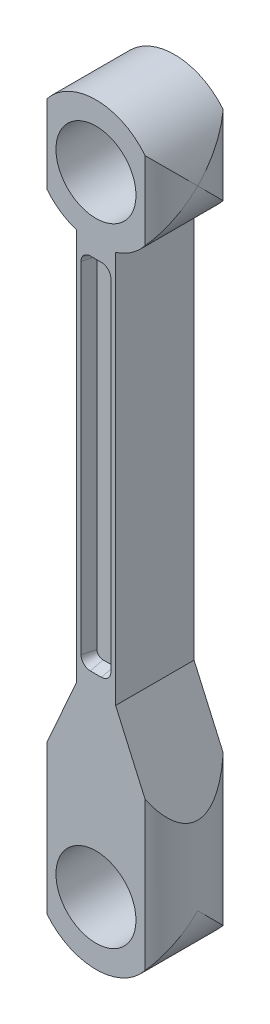
SolidWorks part; units mm, degrees
ref_plane "Front Plane" through (0, 0, 0) normal (0, 0, 1) x (1, 0, 0)
ref_plane "Top Plane" through (0, 0, 0) normal (0, 1, 0) x (1, 0, 0)
ref_plane "Right Plane" through (0, 0, 0) normal (1, 0, 0) x (0, 0, -1)
sketch "Sketch1" plane through (0, 0, 0) normal (0, 0, 1) x (1, 0, 0)
  line L0 (-10.16, 0) -> (-10.16, 12.7)
  line L1 (-10.16, 12.7) -> (-3.1814, 28.448)
  line L2 (-3.1814, 28.448) -> (-3.1814, 91.951)
  line L3 (10.16, 0) -> (10.16, 12.7)
  line L4 (10.16, 12.7) -> (3.1814, 28.448)
  line L5 (3.1814, 28.448) -> (3.1814, 91.951)
  line L6 (10.16, 12.7) -> (10.16, 34.4548) construction
  line L7 (-10.16, 12.7) -> (-10.16, 33.6393) construction
  circle A0 centre (0, 0) radius 6.477
  circle A1 centre (0, 101.6) radius 6.477
  arc A2 (3.1814, 91.951) -> (-3.1814, 91.951) centre (0, 101.6) ccw
  arc A3 (-10.16, 0) -> (10.16, 0) centre (0, 0) ccw
  dimension "D1" = 12.954
  dimension "D2" = 12.954
  dimension "D4" = 20.32
  dimension "D5" = 20.32
  dimension "D3" = 101.6
  dimension "D6" = 23.9
  dimension "D7" = 12.7
  dimension "D8" = 28.448
extrude "Boss-Extrude2" add sketch "Sketch1" along normal blind 12.7
sketch "Sketch3" plane through (0, 0, 12.7) normal (0, 0, 1) x (1, 0, 0)
  line L0 (-3.1814, 91.951) -> (3.1814, 91.951) construction
  line L1 (-3.1814, 28.448) -> (3.1814, 28.448) construction
  line L2 (-3.1814, 91.951) -> (-3.1814, 28.448) construction
  line L3 (-0.8954, 89.408) -> (0.8954, 89.408)
  line L4 (-2.4194, 87.884) -> (-2.4194, 32.766)
  line L5 (-0.8954, 31.242) -> (0.8954, 31.242)
  line L6 (2.4194, 87.884) -> (2.4194, 32.766)
  line L7 (3.1814, 28.448) -> (3.1814, 91.951) construction
  arc A0 (-2.4194, 32.766) -> (-0.8954, 31.242) centre (-0.8954, 32.766) ccw
  arc A1 (0.8954, 31.242) -> (2.4194, 32.766) centre (0.8954, 32.766) ccw
  arc A2 (0.8954, 89.408) -> (2.4194, 87.884) centre (0.8954, 87.884) cw
  arc A3 (-0.8954, 89.408) -> (-2.4194, 87.884) centre (-0.8954, 87.884) ccw
  circle A4 centre (0, 101.6) radius 6.477 construction
  dimension "D5" = 1.524
  dimension "D1" = 12.192
  dimension "D2" = 2.794
  dimension "D3" = 0.762
  dimension "D4" = 0.762
extrude "Cut-Extrude1" cut sketch "Sketch3" against normal blind 2.032 draft 15
sketch "Sketch5" plane through (0, 0, 0) normal (0, 0, -1) x (-1, 0, 0)
  line L0 (3.1814, 91.951) -> (3.1814, 28.448) construction
  line L1 (-3.1814, 28.448) -> (-3.1814, 91.951) construction
  line L2 (-0.8954, 89.408) -> (0.8954, 89.408)
  line L3 (-2.4194, 87.884) -> (-2.4194, 32.766)
  line L4 (-0.8954, 31.242) -> (0.8954, 31.242)
  line L5 (2.4194, 87.884) -> (2.4194, 32.766)
  arc A1 (3.1814, 91.951) -> (-3.1814, 91.951) centre (0, 101.6) ccw construction
  arc A2 (-2.4194, 32.766) -> (-0.8954, 31.242) centre (-0.8954, 32.766) ccw
  arc A3 (0.8954, 31.242) -> (2.4194, 32.766) centre (0.8954, 32.766) ccw
  arc A4 (-0.8954, 89.408) -> (-2.4194, 87.884) centre (-0.8954, 87.884) ccw
  arc A5 (0.8954, 89.408) -> (2.4194, 87.884) centre (0.8954, 87.884) cw
  dimension "D5" = 1.524
  dimension "D1" = 31.242
  dimension "D2" = 12.192
  dimension "D3" = 0.762
  dimension "D4" = 0.762
extrude "Cut-Extrude2" cut sketch "Sketch5" against normal blind 2.032 draft 15
sketch "Sketch6" plane through (0, 0, 0) normal (0, 1, 0) x (1, 0, 0)
  line L0 (-10.16, -6.3884) -> (10.16, -6.3884) construction
  circle A0 centre (0, -6.3884) radius 10.16
  circle A1 centre (0, -6.3884) radius 15.3084
  dimension "D1" = 20.32
  dimension "D2" = 30.6169
extrude "Cut-Extrude3" cut sketch "Sketch6" against normal through all both and the other way through all
